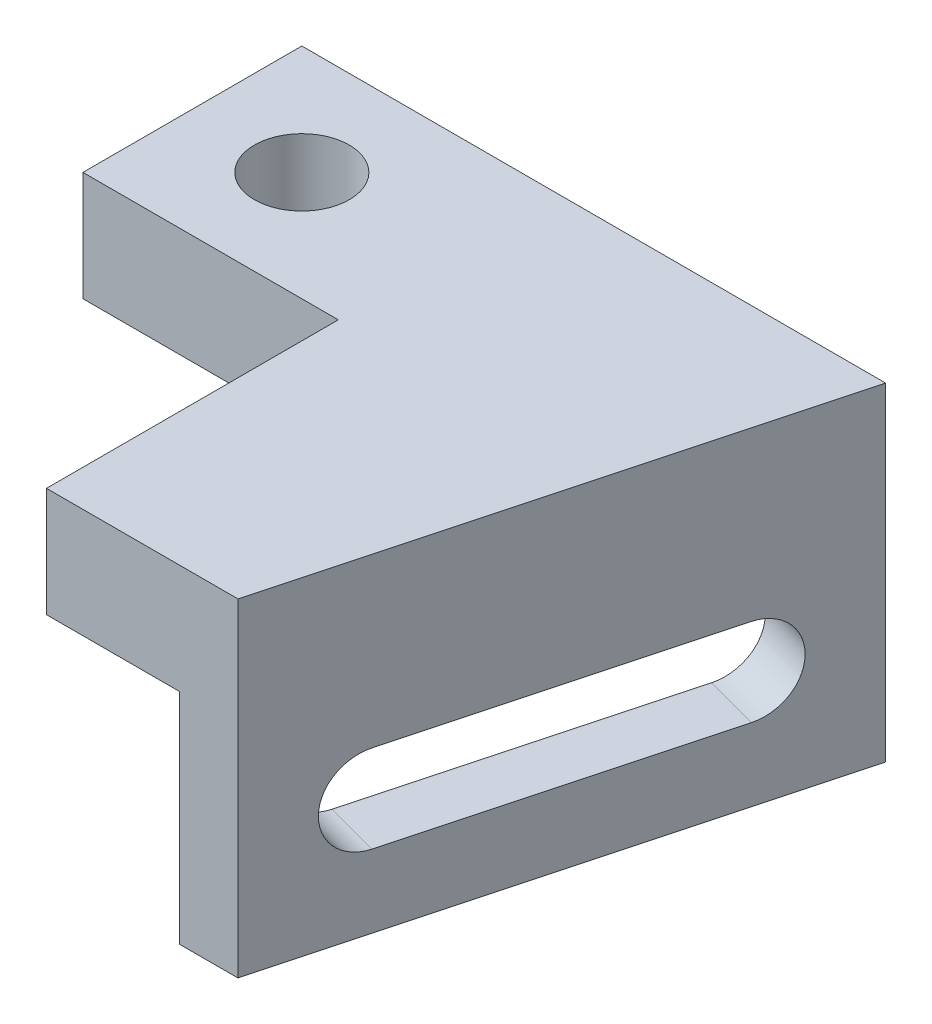
SolidWorks part; units mm, degrees
ref_plane "Front Plane" through (0, 0, 0) normal (0, 0, 1) x (1, 0, 0)
ref_plane "Top Plane" through (0, 0, 0) normal (0, 1, 0) x (1, 0, 0)
ref_plane "Right Plane" through (0, 0, 0) normal (1, 0, 0) x (0, 0, -1)
sketch "Sketch1" plane through (0, 0, 0) normal (0, 1, 0) x (1, 0, 0)
  line L0 (45, 30) -> (26.2436, -40)
  line L1 (45, 30) -> (-35, 30)
  line L3 (26.2436, -40) -> (0, -40)
  line L4 (-35, 30) -> (-35, 0)
  line L7 (-35, 0) -> (0, 0)
  line L8 (0, 0) -> (0, -40)
  circle A0 centre (-20, 15) radius 6.5
  point P0 (0, 0)
  dimension "D5" = 13
  dimension "D6" = 15
  dimension "D1" = 80
  dimension "D2" = 30
  dimension "D3" = 70
  dimension "D4" = 35
  dimension "D7" = 75
  dimension "D8" = 15
extrude "Boss-Extrude1" add sketch "Sketch1" along normal blind 15
sketch "Sketch5" plane through (0, 0, 0) normal (0, -1, 0) x (1, 0, 0)
  line L0 (18.2436, 40) -> (37, -30)
  line L6 (-35, -30) -> (45, -30)
  line L7 (45, -30) -> (26.2436, 40)
  line L8 (26.2436, 40) -> (0, 40)
  line L9 (0, 40) -> (0, 0)
  line L10 (0, 0) -> (-35, 0)
  line L11 (-35, 0) -> (-35, -30)
  line L12 (37, -30) -> (45, -30)
  line L13 (45, -30) -> (26.2436, 40)
  line L14 (26.2436, 40) -> (18.2436, 40)
  dimension "D2" = 8
  dimension "D1" = 0
extrude "Boss-Extrude3" add sketch "Sketch5" along normal blind 30
sketch "Sketch7" plane through (34.4856, 0, 9.2404) normal (0.9659, 0, 0.2588) x (0.2588, 0, -0.9659)
  line L0 (-16.8447, -14) -> (25.6246, -14) construction
  line L1 (-16.8447, -8) -> (25.6246, -8)
  line L2 (-16.8447, -20) -> (25.6246, -20)
  line L3 (-31.8447, -5.533) -> (40.6246, -5.533)
  line L4 (-31.8447, 15) -> (-31.8447, -30)
  line L5 (-31.8447, -30) -> (40.6246, -30)
  line L6 (40.6246, -30) -> (40.6246, 15)
  line L7 (40.6246, 15) -> (-31.8447, 15)
  line L8 (-31.8447, 15) -> (-31.8447, -30)
  line L9 (-31.8447, -30) -> (40.6246, -30)
  line L10 (40.6246, -30) -> (40.6246, 15)
  line L11 (40.6246, 15) -> (-31.8447, 15)
  arc A0 (-16.8447, -8) -> (-16.8447, -20) centre (-16.8447, -14) ccw
  arc A1 (25.6246, -20) -> (25.6246, -8) centre (25.6246, -14) ccw
  point P6 (4.39, -14)
  point P13 (0, 0)
  dimension "D2" = 15
  dimension "D3" = 15
  dimension "D4" = 10
  dimension "D5" = 6
  dimension "D1" = 0
extrude "Cut-Extrude1" cut sketch "Sketch7" against normal blind 10
